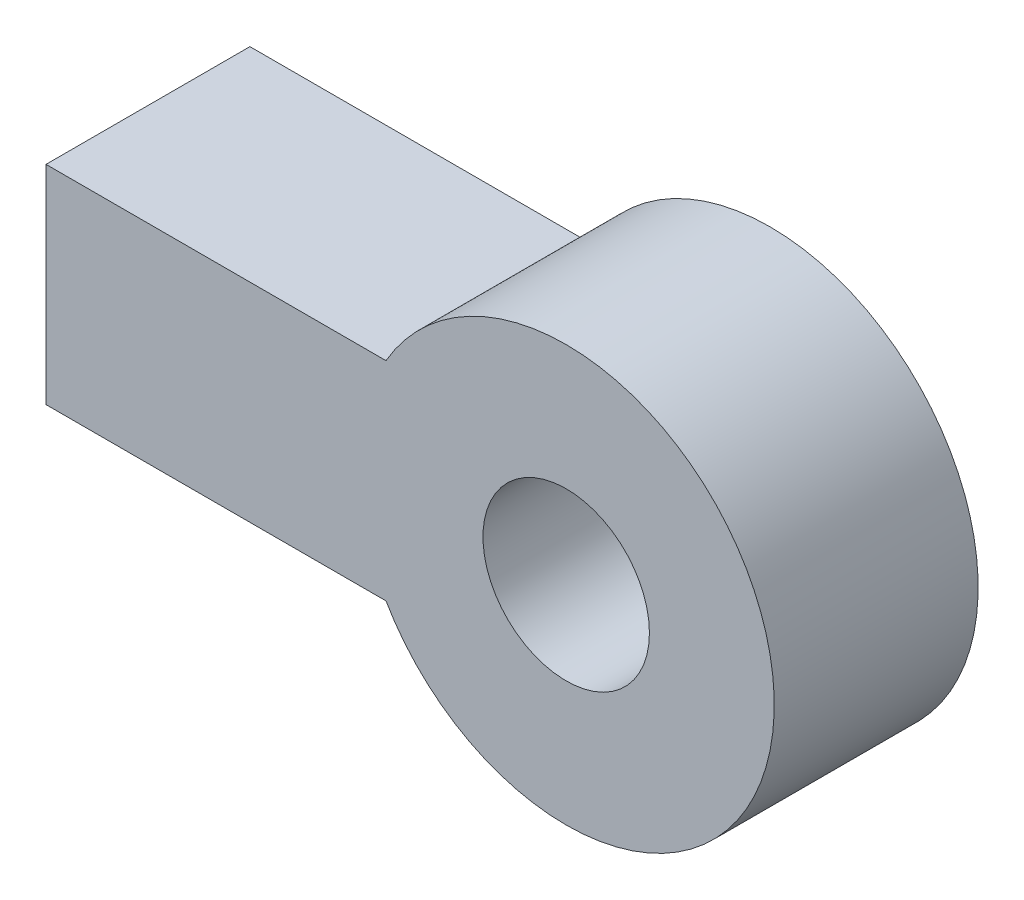
SolidWorks part; units mm, degrees
ref_plane "Front Plane" through (0, 0, 0) normal (0, 0, 1) x (1, 0, 0)
ref_plane "Top Plane" through (0, 0, 0) normal (0, 1, 0) x (1, 0, 0)
ref_plane "Right Plane" through (0, 0, 0) normal (1, 0, 0) x (0, 0, -1)
sketch "Sketch3" plane through (0, 0, 0) normal (0, 0, 1) x (1, 0, 0)
  line L2 (-10.9985, -6.35) -> (-19.05, -6.35)
  line L4 (-19.05, 6.35) -> (-10.9985, 6.35)
  line L5 (-19.05, -6.35) -> (-31.75, -6.35)
  line L6 (-31.75, -6.35) -> (-31.75, 6.35)
  line L7 (-31.75, 6.35) -> (-19.05, 6.35)
  arc A2 (-10.9985, -6.35) -> (-10.9985, 6.35) centre (0, 0) ccw
extrude "Boss-Extrude2" add sketch "Sketch3" along normal blind 12.446 contours L7 L4 A2 L2 L5 L6
sketch "Sketch4" plane through (0, 0, 0) normal (0, 0, -1) x (-1, 0, 0)
  circle A0 centre (0, 0) radius 2.54
extrude "Cut-Extrude1" cut sketch "Sketch4" against normal through all
sketch "Sketch5" plane through (0, 0, 12.446) normal (0, 0, 1) x (1, 0, 0)
  circle A0 centre (0, 0) radius 5.08
extrude "Cut-Extrude2" cut sketch "Sketch5" against normal blind 10.16
